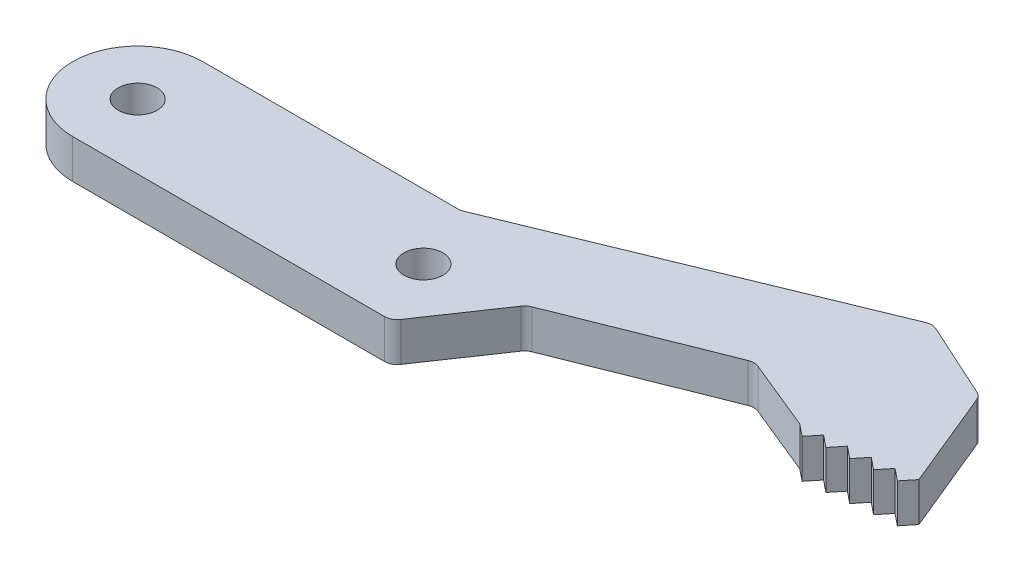
SolidWorks part; units mm, degrees
ref_plane "Front Plane" through (0, 0, 0) normal (0, 0, 1) x (1, 0, 0)
ref_plane "Top Plane" through (0, 0, 0) normal (0, 1, 0) x (1, 0, 0)
ref_plane "Right Plane" through (0, 0, 0) normal (1, 0, 0) x (0, 0, -1)
sketch "Sketch1" plane through (0, 0, 0) normal (0, 1, 0) x (1, 0, 0)
  line L1 (0, -5) -> (23.9989, -5)
  line L2 (0, 5) -> (19.6524, 5)
  line L3 (20.0327, 5.0751) -> (45.2294, 15.4347)
  line L4 (46.0242, 15.4199) -> (51.8314, 12.7746)
  line L5 (52.3417, 12.2448) -> (55.4426, 4.7029)
  line L6 (24.8266, -4.5611) -> (28.5649, 0.9541)
  line L7 (29.0223, 1.322) -> (40.9296, 6.07)
  line L8 (41.6788, 6.0666) -> (47.1446, 3.8294)
  line L11 (47.1446, 3.8294) -> (48.0617, 3.087)
  line L12 (48.0617, 3.087) -> (48.8042, 4.0041)
  line L13 (48.8042, 4.0041) -> (49.7213, 3.2617)
  line L14 (49.7213, 3.2617) -> (50.4638, 4.1788)
  line L15 (50.4638, 4.1788) -> (51.3809, 3.4364)
  line L16 (51.3809, 3.4364) -> (52.1234, 4.3535)
  line L17 (52.1234, 4.3535) -> (53.0405, 3.6111)
  line L18 (53.0405, 3.6111) -> (53.783, 4.5282)
  line L19 (53.783, 4.5282) -> (54.7001, 3.7858)
  line L20 (54.7001, 3.7858) -> (55.4426, 4.7029)
  circle A0 centre (0, 0) radius 1.5
  arc A1 (0, 5) -> (0, -5) centre (0, 0) ccw
  circle A2 centre (22, 0) radius 1.5
  arc A3 (28.5649, 0.9541) -> (29.0223, 1.322) centre (29.3927, 0.3931) cw
  arc A4 (40.9296, 6.07) -> (41.6788, 6.0666) centre (41.2999, 5.1412) cw
  arc A5 (51.8314, 12.7746) -> (52.3417, 12.2448) centre (51.4169, 11.8646) cw
  arc A6 (45.2294, 15.4347) -> (46.0242, 15.4199) centre (45.6096, 14.5098) cw
  arc A7 (19.6524, 5) -> (20.0327, 5.0751) centre (19.6524, 6) ccw
  arc A8 (23.9989, -5) -> (24.8266, -4.5611) centre (23.9989, -4) ccw
  point P27 (28.7372, 1.2083)
  point P30 (41.3048, 6.2197)
  point P33 (52.1913, 12.6106)
  point P36 (45.63, 15.5994)
  point P39 (19.85, 5)
  point P42 (24.5291, -5)
  dimension "D1" = 3
  dimension "D2" = 10
  dimension "D4" = 3
  dimension "D20" = 1
  dimension "D3" = 22
  dimension "D5" = 124.13
  dimension "D6" = 7.5
  dimension "D7" = 214.13
  dimension "D8" = 13.53
  dimension "D9" = 224
  dimension "D10" = 6.31
  dimension "D11" = 157.65
  dimension "D12" = 19.85
  dimension "D13" = 25.78
  dimension "D14" = 7.21
  dimension "D15" = 133.16
  dimension "D16" = 136.84
  dimension "D17" = 8.55
  dimension "D18" = 1.18
  dimension "D19" = 1.18
extrude "Boss-Extrude1" add sketch "Sketch1" along normal blind 3
scale "Scale1" scale about centroid uniform scaling yes scale factor 1.8
